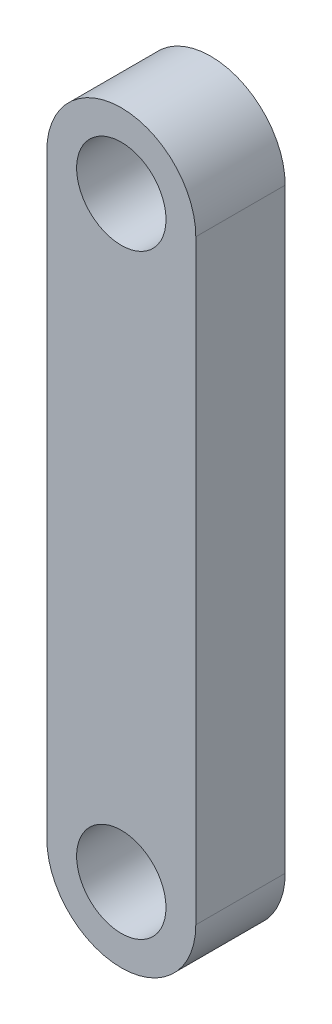
SolidWorks part; units mm, degrees
ref_plane "Front Plane" through (0, 0, 0) normal (0, 0, 1) x (1, 0, 0)
ref_plane "Top Plane" through (0, 0, 0) normal (0, 1, 0) x (1, 0, 0)
ref_plane "Right Plane" through (0, 0, 0) normal (1, 0, 0) x (0, 0, -1)
sketch "Sketch1" plane through (0, 0, 0) normal (0, 0, 1) x (1, 0, 0)
  line L0 (0, -50) -> (0, 50) construction
  line L1 (-12.5, -50) -> (-12.5, 50)
  line L2 (12.5, -50) -> (12.5, 50)
  arc A0 (-12.5, -50) -> (12.5, -50) centre (0, -50) ccw
  arc A1 (12.5, 50) -> (-12.5, 50) centre (0, 50) ccw
  circle A2 centre (0, 50) radius 7.5
  circle A3 centre (0, -50) radius 7.5
  point P3 (0, 0)
  dimension "D3" = 15
  dimension "D1" = 25
  dimension "D2" = 100
extrude "Boss-Extrude1" add sketch "Sketch1" along normal blind 15
